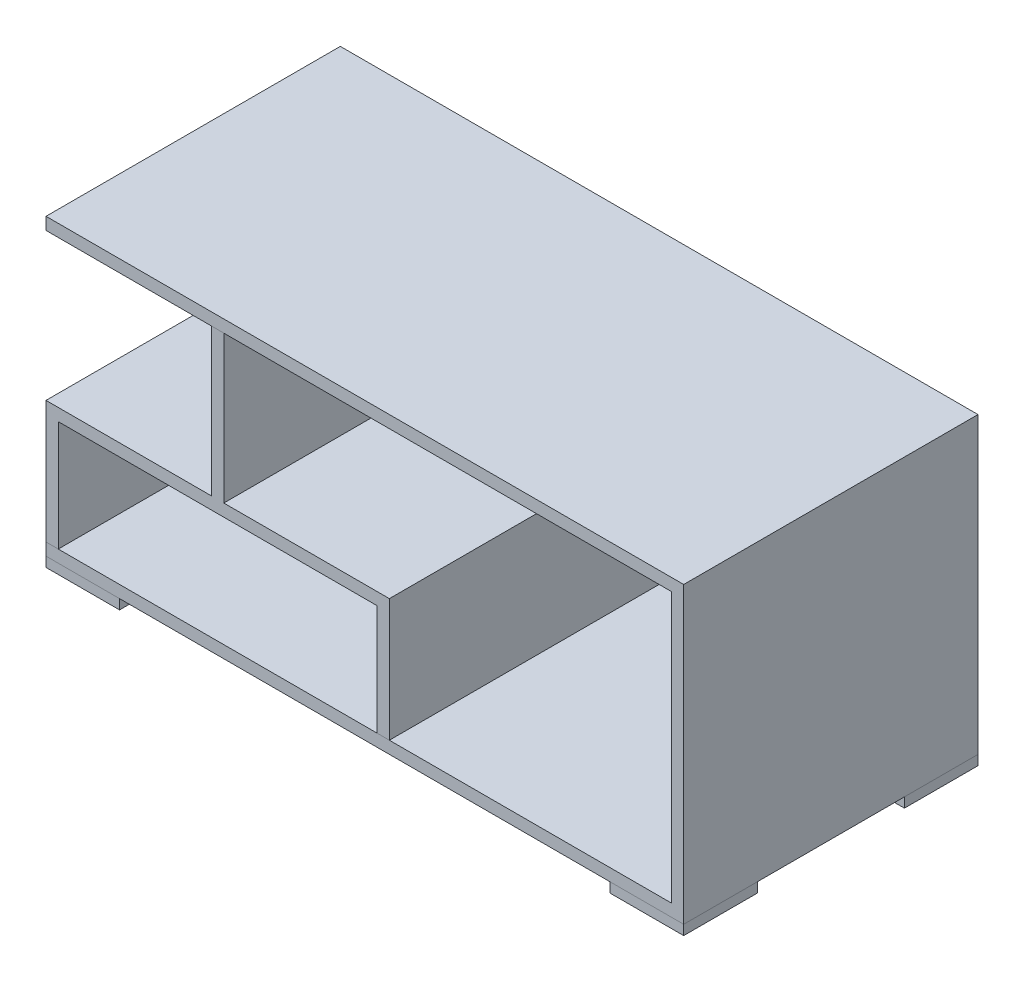
SolidWorks part; units mm, degrees
ref_plane "Front Plane" through (0, 0, 0) normal (0, 0, 1) x (1, 0, 0)
ref_plane "Top Plane" through (0, 0, 0) normal (0, 1, 0) x (1, 0, 0)
ref_plane "Right Plane" through (0, 0, 0) normal (1, 0, 0) x (0, 0, -1)
sketch "Sketch1" plane through (0, 0, 0) normal (0, 0, 1) x (1, 0, 0)
  line L0 (0, 0) -> (-64557.6834, 0) construction
  line L1 (0, 0) -> (0, -64557.6834) construction
  line L2 (-650, 0) -> (650, 0)
  line L3 (650, 0) -> (650, 600)
  line L4 (650, 600) -> (-650, 600)
  line L5 (-650, 600) -> (-650, 575)
  line L6 (-650, 575) -> (625, 575)
  line L7 (625, 575) -> (625, 25)
  line L8 (625, 25) -> (-650, 25)
  line L9 (-650, 25) -> (-650, 0)
  dimension "D1" = 25
  dimension "D2" = 25
  dimension "D3" = 25
  dimension "D4" = 1300
  dimension "D5" = 600
extrude "Boss-Extrude1" add sketch "Sketch1" along normal mid plane 600
sketch "Sketch2" plane through (0, 0, 300) normal (0, 0, 1) x (1, 0, 0)
  line L0 (-312.5, 575) -> (-312.5, 275)
  line L1 (-650, 575) -> (625, 575) construction
  line L2 (-312.5, 275) -> (-650, 275)
  line L3 (-650, 275) -> (-650, 25)
  line L4 (-650, 25) -> (-625, 25)
  line L5 (625, 25) -> (-650, 25) construction
  line L6 (-625, 25) -> (-625, 250)
  line L7 (-625, 250) -> (25, 250)
  line L8 (25, 250) -> (25, 25)
  line L9 (25, 25) -> (50, 25)
  line L10 (50, 25) -> (50, 275)
  line L11 (50, 275) -> (-287.5, 275)
  line L12 (-287.5, 275) -> (-287.5, 575)
  line L13 (-287.5, 575) -> (-312.5, 575)
  dimension "D1" = 25
  dimension "D2" = 25
  dimension "D3" = 25
  dimension "D4" = 700
  dimension "D5" = 300
  dimension "D6" = 25
extrude "Boss-Extrude2" add sketch "Sketch2" against normal blind 600 separate body
sketch "Sketch3" plane through (0, 0, 0) normal (0, -1, 0) x (1, 0, 0)
  line L0 (-650, 300) -> (650, 300) construction
  line L1 (-650, 300) -> (-500, 300)
  line L2 (-650, 300) -> (-650, 150)
  line L3 (-650, 150) -> (-500, 150)
  line L4 (-500, 300) -> (-500, 150)
  line L5 (0, 0) -> (-50000, 0) construction
  line L6 (0, 0) -> (0, -50000) construction
  line L7 (-650, 300) -> (-650, -300) construction
  line L8 (-650, -150) -> (-500, -150)
  line L9 (-500, -300) -> (-500, -150)
  line L10 (-650, -300) -> (-500, -300)
  line L11 (-650, -300) -> (-650, -150)
  line L12 (650, 150) -> (500, 150)
  line L13 (500, 300) -> (500, 150)
  line L14 (650, 300) -> (500, 300)
  line L15 (650, 300) -> (650, 150)
  line L16 (650, -300) -> (650, -150)
  line L17 (650, -300) -> (500, -300)
  line L18 (500, -300) -> (500, -150)
  line L19 (650, -150) -> (500, -150)
  dimension "D1" = 150
  dimension "D2" = 150
extrude "Boss-Extrude3" add sketch "Sketch3" along normal blind 20 separate body
